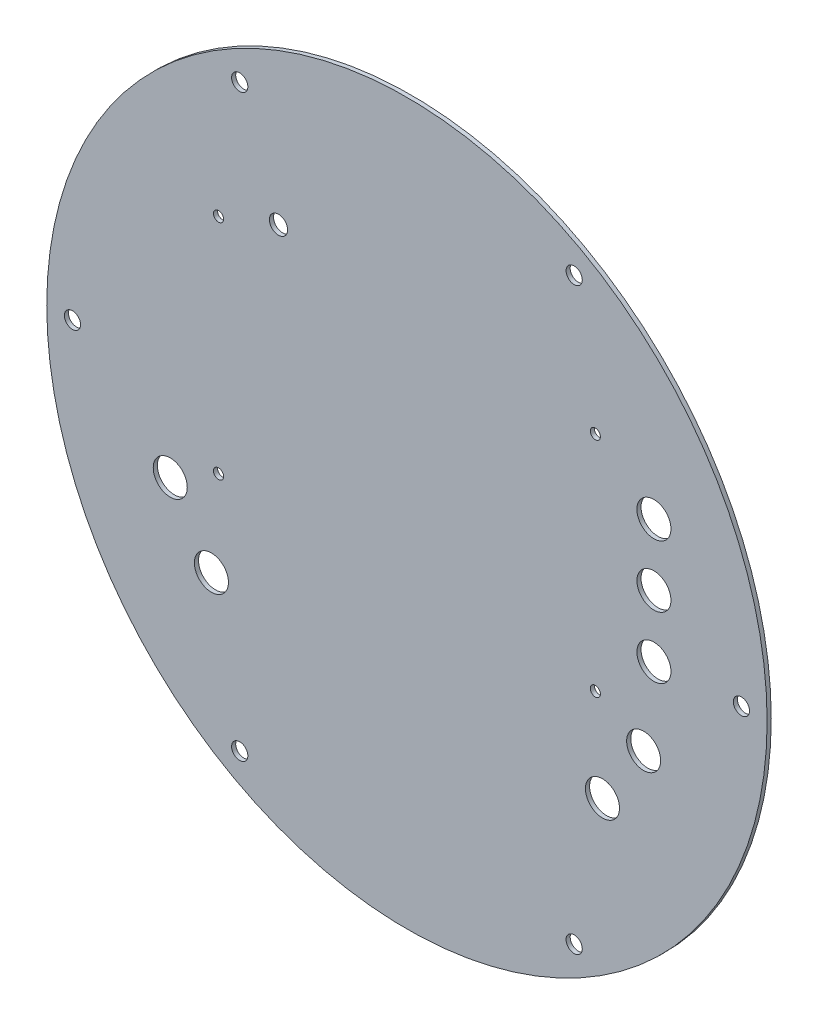
SolidWorks part; units mm, degrees
ref_plane "Front Plane" through (0, 0, 0) normal (0, 0, 1) x (1, 0, 0)
ref_plane "Top Plane" through (0, 0, 0) normal (0, 1, 0) x (1, 0, 0)
ref_plane "Right Plane" through (0, 0, 0) normal (1, 0, 0) x (0, 0, -1)
sketch "Sketch1" plane through (0, 0, 0) normal (0, 0, 1) x (1, 0, 0)
  line L0 (0, 0) -> (0, 126.7891) construction
  line L1 (0, 0) -> (41.275, 71.4904) construction
  circle A0 centre (0, 0) radius 88.9
  circle A1 centre (0, 0) radius 82.55 construction
  circle A2 centre (41.275, 71.4904) radius 2
  circle A3 centre (82.55, 0) radius 2
  circle A4 centre (41.275, -71.4904) radius 2
  circle A5 centre (-41.275, -71.4904) radius 2
  circle A6 centre (-82.55, 0) radius 2
  circle A7 centre (-41.275, 71.4904) radius 2
  point P30 (0, 0)
  dimension "D1" = 177.8
  dimension "D2" = 165.1
  dimension "D3" = 4
  dimension "D5" = 30
  dimension "D4" = 6
extrude "Boss-Extrude1" add sketch "Sketch1" along normal blind 1.016
sketch "Sketch3" plane through (0, 0, 1.016) normal (0, 0, 1) x (1, 0, 0)
  line L0 (-48.7, -7.4) -> (-48.7, 32.8) construction
  line L1 (-48.7, -7.4) -> (48.7, -7.4) construction
  line L2 (-48.7, 32.8) -> (48.7, 32.8) construction
  line L3 (48.7, -7.4) -> (48.7, 32.8) construction
  line L4 (-48.7, -7.4) -> (48.7, 32.8) construction
  line L5 (-48.7, 32.8) -> (48.7, -7.4) construction
  line L6 (-46.5, -14.8) -> (-46.5, 40.2) construction
  line L7 (-46.5, -14.8) -> (46.5, -14.8) construction
  line L8 (-46.5, 40.2) -> (46.5, 40.2) construction
  line L9 (46.5, -14.8) -> (46.5, 40.2) construction
  line L10 (-46.5, -14.8) -> (46.5, 40.2) construction
  line L11 (-46.5, 40.2) -> (46.5, -14.8) construction
  circle A0 centre (-46.5, 40.2) radius 1.25
  circle A1 centre (46.5, 40.2) radius 1.25
  circle A2 centre (46.5, -14.8) radius 1.25
  circle A3 centre (-46.5, -14.8) radius 1.25
  circle A4 centre (-31.7, 45.8) radius 2.25
  point P1 (0, 12.7)
  point P2 (0, 12.7)
  dimension "D5" = 2.5
  dimension "D7" = 4.5
  dimension "D1" = 40.2
  dimension "D2" = 97.4
  dimension "D3" = 93
  dimension "D4" = 55
  dimension "D6" = 12.7
  dimension "D8" = 13
  dimension "D9" = 17
extrude "Cut-Extrude2" cut sketch "Sketch3" against normal blind 3.175
sketch "Sketch4" plane through (0, 0, 1.016) normal (0, 0, 1) x (1, 0, 0)
  line L0 (60.96, 29.21) -> (60.96, -1.27) construction
  line L2 (0, 0) -> (0, 57.6622) construction
  circle A0 centre (60.96, 29.21) radius 4.2
  circle A1 centre (60.96, 13.97) radius 4.2
  circle A2 centre (60.96, -1.27) radius 4.2
  circle A6 centre (58.42, -21.59) radius 4.2
  circle A7 centre (48.26, -36.83) radius 4.2
  circle A8 centre (-58.42, -21.59) radius 4.2
  circle A9 centre (-48.26, -36.83) radius 4.2
  point P3 (60.96, 13.97)
  dimension "D3" = 8.4
  dimension "D4" = 58.42
  dimension "D5" = 48.26
  dimension "D7" = 21.59
  dimension "D1" = 60.96
  dimension "D2" = 30.48
  dimension "D6" = 13.97
  dimension "D8" = 36.83
extrude "Cut-Extrude3" cut sketch "Sketch4" against normal blind 10
